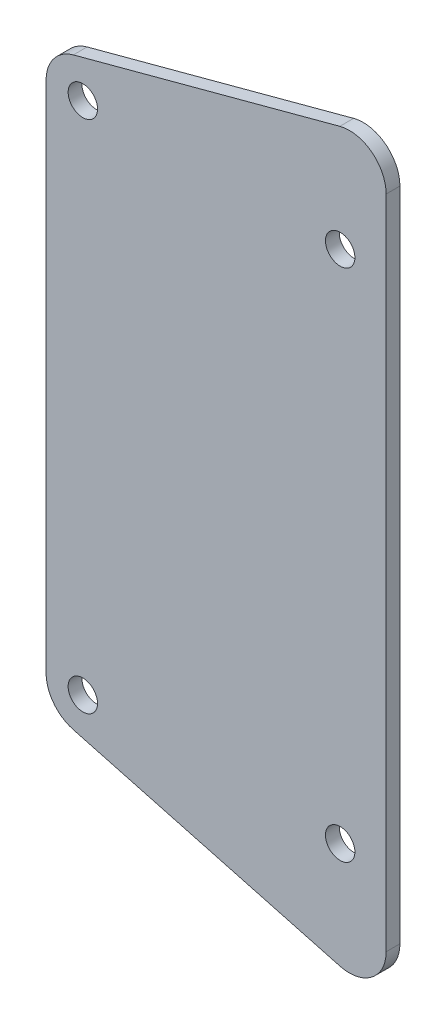
SolidWorks part; units mm, degrees
ref_plane "Front" through (0, 0, 0) normal (0, 0, 1) x (1, 0, 0)
ref_plane "Top" through (0, 0, 0) normal (0, 1, 0) x (1, 0, 0)
ref_plane "Right" through (0, 0, 0) normal (1, 0, 0) x (0, 0, -1)
sketch "Sketch1" plane through (0, 0, 0) normal (0, 0, 1) x (1, 0, 0)
  line L7 (5, 59) -> (-32, 72.4669)
  line L9 (-32, 56) -> (-32, 72.4669)
  line L10 (-32, 0) -> (-32, -16.4669)
  line L12 (5, -3) -> (-32, -16.4669)
  line L16 (-32, 0) -> (-32, 56)
  line L17 (5, 59) -> (5, -3)
  circle A0 centre (0, 0) radius 1.6
  circle A1 centre (-28, 0) radius 1.6
  circle A2 centre (0, 56) radius 1.6
  circle A3 centre (-28, 56) radius 1.6
extrude "Boss-Extrude1" add sketch "Sketch1" along normal blind 1.5
sketch "Sketch2" plane through (0, 0, 1.5) normal (0, 0, 1) x (1, 0, 0)
  line L0 (5, 59) -> (-43.8757, 59)
  line L1 (-43.8757, 59) -> (-43.8757, 79.1454)
  line L2 (-43.8757, 79.1454) -> (45.9159, 71.4717)
  line L3 (45.9159, 71.4717) -> (5, 59)
  line L4 (5, -3) -> (-36.9076, -3)
  line L5 (-36.9076, -3) -> (-45.5515, -23.4357)
  line L6 (-45.5515, -23.4357) -> (23.1593, -21.407)
  line L7 (23.1593, -21.407) -> (5, -3)
extrude "Cut-Extrude1" cut sketch "Sketch2" against normal blind 1.5
sketch "Sketch3" plane through (0, 0, 1.5) normal (0, 0, 1) x (1, 0, 0)
  line L0 (-32, 59) -> (5, 68.9141)
  line L1 (-32, 59) -> (5, 59)
  line L2 (5, 59) -> (5, 68.9141)
  line L5 (5, -3) -> (5, -12.9141)
  line L6 (-32, -3) -> (5, -3)
  line L7 (-32, -3) -> (5, -12.9141)
extrude "Boss-Extrude2" add sketch "Sketch3" against normal up to surface (1.5 mm away) up to face at (-13.5, 28, 0)
fillet "Fillet1" radius 4 4 edges at (-32, 59, 0.75) (-32, -3, 0.75) (5, -12.9141, 0.75) (5, 68.9141, 0.75)
